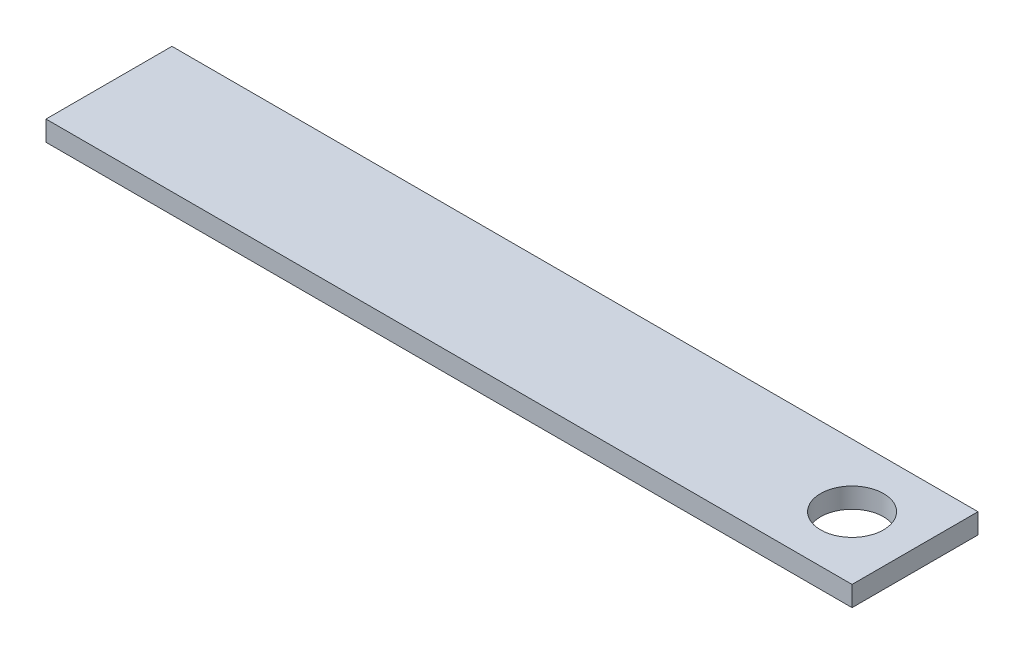
SolidWorks part; units mm, degrees
ref_plane "Front Plane" through (0, 0, 0) normal (0, 0, 1) x (1, 0, 0)
ref_plane "Top Plane" through (0, 0, 0) normal (0, 1, 0) x (1, 0, 0)
ref_plane "Right Plane" through (0, 0, 0) normal (1, 0, 0) x (0, 0, -1)
sketch "Sketch1" plane through (0, 0, 0) normal (0, 1, 0) x (1, 0, 0)
  line L1 (-80, 12.5) -> (80, 12.5)
  line L2 (-80, 12.5) -> (-80, -12.5)
  line L3 (-80, -12.5) -> (80, -12.5)
  line L4 (80, 12.5) -> (80, -12.5)
  line L5 (-80, 12.5) -> (80, -12.5) construction
  line L6 (-80, -12.5) -> (80, 12.5) construction
  circle A4 centre (67.5, 0) radius 6.25
  point P0 (0, 0)
  point P17 (80, 0)
  dimension "D3" = 12.5
  dimension "D4" = 12.5
  dimension "D1" = 25
  dimension "D2" = 160
extrude "Boss-Extrude1" add sketch "Sketch1" along normal blind 4
